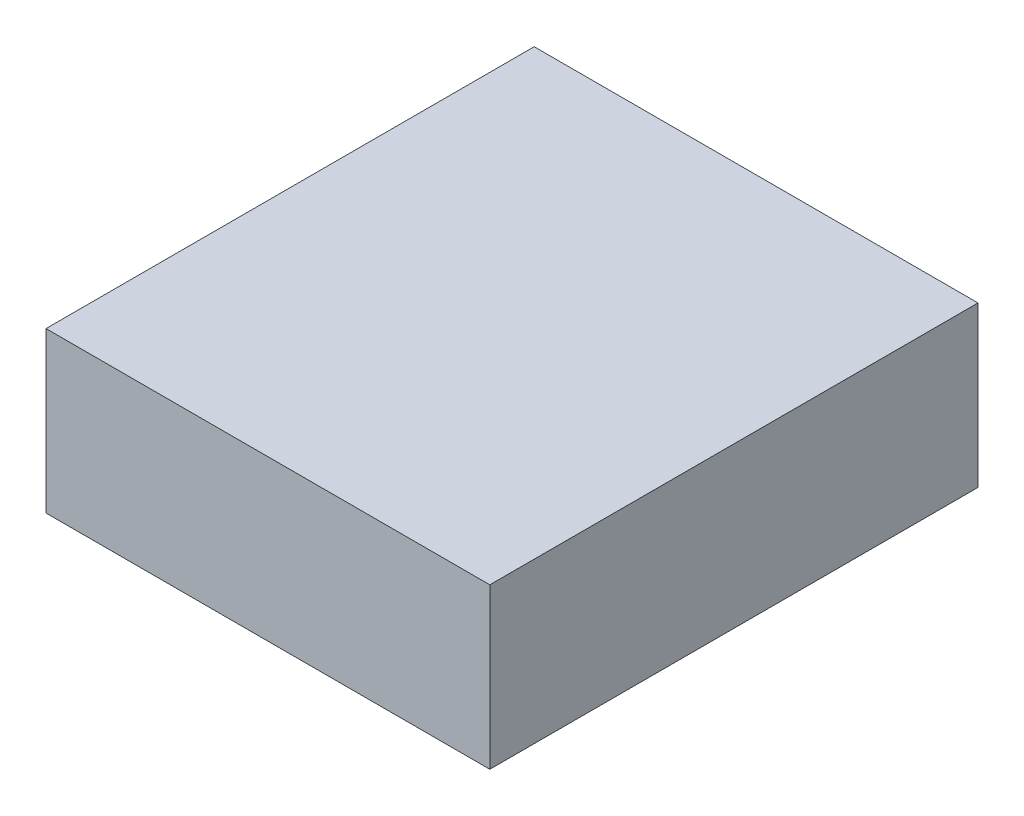
SolidWorks part; units mm, degrees
ref_plane "Front Plane" through (0, 0, 0) normal (0, 0, 1) x (1, 0, 0)
ref_plane "Top Plane" through (0, 0, 0) normal (0, 1, 0) x (1, 0, 0)
ref_plane "Right Plane" through (0, 0, 0) normal (1, 0, 0) x (0, 0, -1)
sketch "Sketch1" plane through (0, 0, 0) normal (0, 1, 0) x (1, 0, 0)
  line L1 (-12500, -13750) -> (12500, -13750)
  line L2 (-12500, -13750) -> (-12500, 13750)
  line L3 (-12500, 13750) -> (12500, 13750)
  line L4 (12500, -13750) -> (12500, 13750)
  line L5 (-12500, -13750) -> (12500, 13750) construction
  line L6 (-12500, 13750) -> (12500, -13750) construction
  point P0 (0, 0)
  dimension "D1" = 25000
  dimension "D2" = 27500
extrude "Boss-Extrude1" add sketch "Sketch1" along normal mid plane 9000
